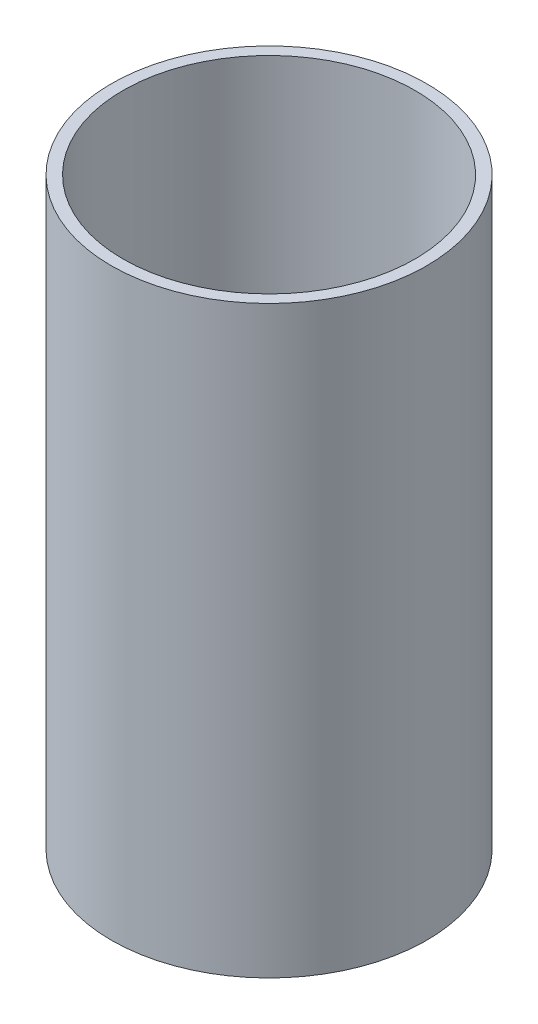
SolidWorks part; units mm, degrees
ref_plane "Front Plane" through (0, 0, 0) normal (0, 0, 1) x (1, 0, 0)
ref_plane "Top Plane" through (0, 0, 0) normal (0, 1, 0) x (1, 0, 0)
ref_plane "Right Plane" through (0, 0, 0) normal (1, 0, 0) x (0, 0, -1)
sketch "Sketch1" plane through (0, 0, 0) normal (0, 1, 0) x (1, 0, 0)
  circle A0 centre (0, 0) radius 27
  circle A1 centre (0, 0) radius 25
  dimension "D1" = 50
  dimension "D2" = 54
extrude "Boss-Extrude1" add sketch "Sketch1" along normal blind 100
